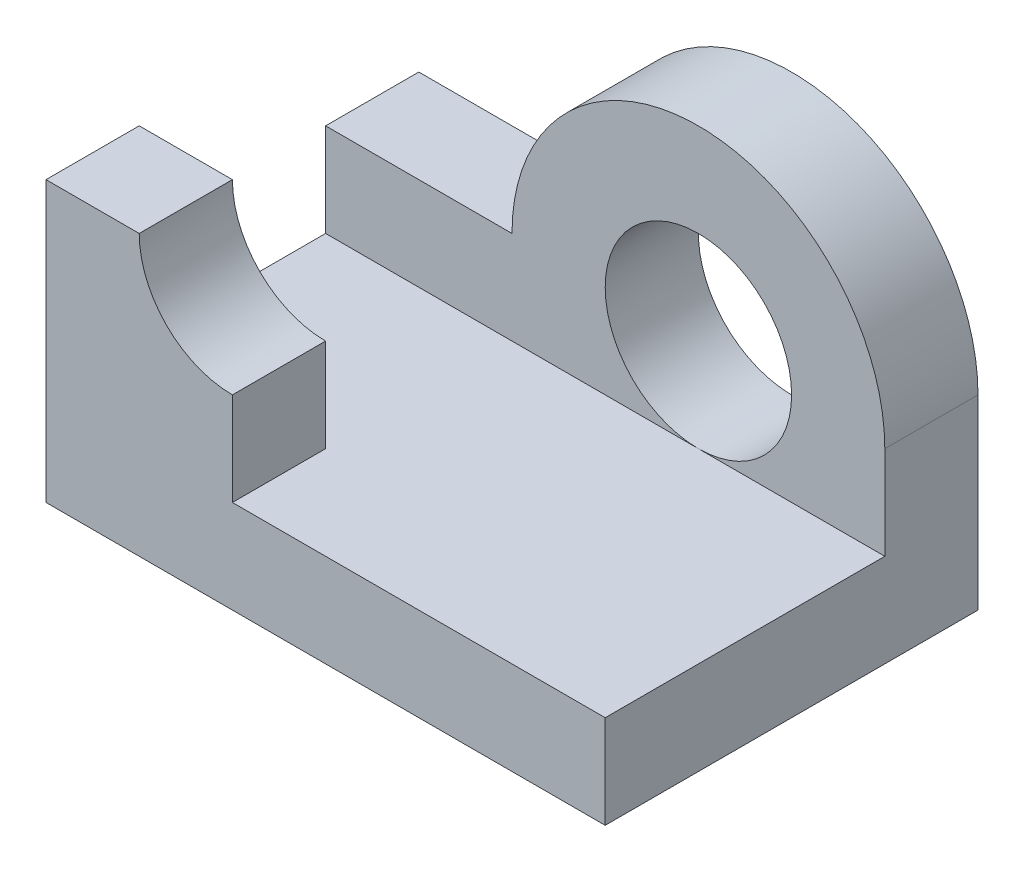
SolidWorks part; units mm, degrees
ref_plane "Front Plane" through (0, 0, 0) normal (0, 0, 1) x (1, 0, 0)
ref_plane "Top Plane" through (0, 0, 0) normal (0, 1, 0) x (1, 0, 0)
ref_plane "Right Plane" through (0, 0, 0) normal (1, 0, 0) x (0, 0, -1)
sketch "Sketch1" plane through (0, 0, 0) normal (0, 1, 0) x (1, 0, 0)
  line L1 (0, 0) -> (-60, 0)
  line L2 (0, 0) -> (0, 40)
  line L3 (0, 40) -> (-60, 40)
  line L4 (-60, 0) -> (-60, 40)
  dimension "D1" = 60
  dimension "D2" = 40
extrude "Boss-Extrude1" add sketch "Sketch1" along normal blind 10
sketch "Sketch2" plane through (0, 0, -40) normal (0, 0, -1) x (-1, 0, 0)
  line L0 (0, 10) -> (0, 20)
  line L1 (40, 20) -> (60, 20)
  line L2 (60, 20) -> (60, 10)
  line L3 (60, 10) -> (0, 10)
  arc A0 (0, 20) -> (40, 20) centre (20, 20) cw
  dimension "D1" = 20
  dimension "D2" = 10
extrude "Boss-Extrude2" add sketch "Sketch2" against normal blind 10
sketch "Sketch3" plane through (0, 0, -30) normal (0, 0, 1) x (1, 0, 0)
  circle A0 centre (-20, 20) radius 10
  dimension "D1" = 20
extrude "Cut-Extrude1" cut sketch "Sketch3" against normal blind 10
sketch "Sketch4" plane through (0, 0, 0) normal (0, 0, 1) x (1, 0, 0)
  line L0 (-60, 10) -> (-60, 30)
  line L1 (-60, 30) -> (-50, 30)
  line L2 (-40, 20) -> (-40, 10)
  line L3 (-20, 10) -> (-60, 10) construction
  line L4 (-40, 10) -> (-60, 10)
  arc A0 (-50, 30) -> (-40, 20) centre (-40, 30) ccw
  dimension "D2" = 10
  dimension "D1" = 10
  dimension "D3" = 20
extrude "Boss-Extrude3" add sketch "Sketch4" against normal blind 10
